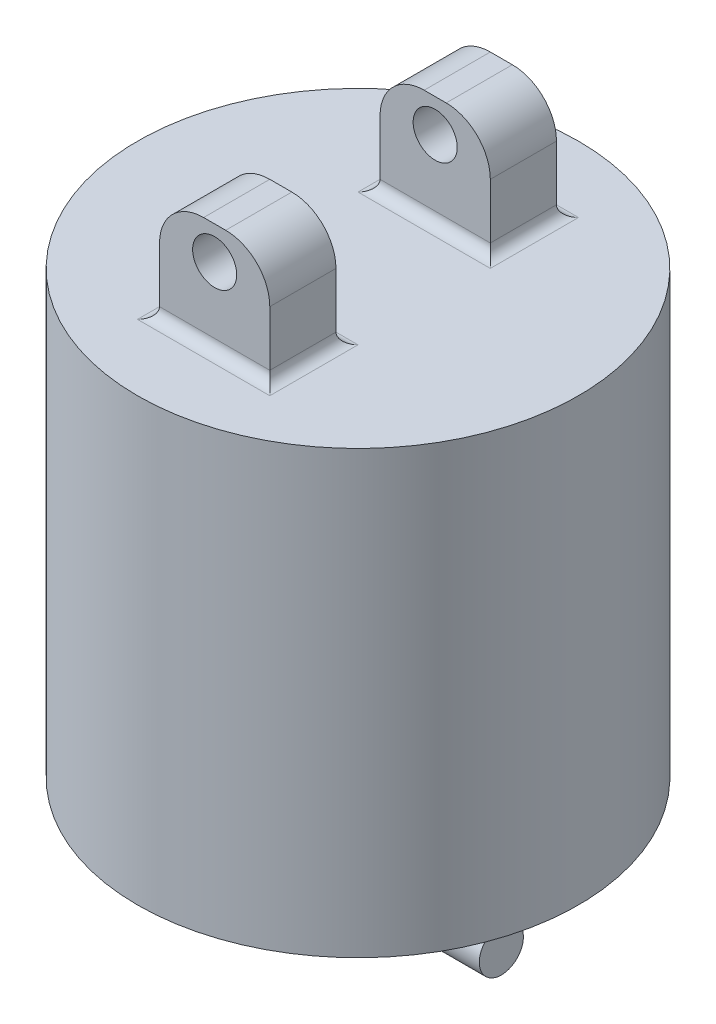
SolidWorks part; units mm, degrees
ref_plane "Front Plane" through (0, 0, 0) normal (0, 0, 1) x (1, 0, 0)
ref_plane "Top Plane" through (0, 0, 0) normal (0, 1, 0) x (1, 0, 0)
ref_plane "Right Plane" through (0, 0, 0) normal (1, 0, 0) x (0, 0, -1)
sketch "Sketch1" plane through (0, 0, 0) normal (0, 1, 0) x (1, 0, 0)
  circle A0 centre (0, 0) radius 50
  dimension "D1" = 100
extrude "Boss-Extrude1" add sketch "Sketch1" along normal blind 100
sketch "Sketch6" plane through (0, 100, 0) normal (0, 1, 0) x (1, 0, 0)
  line L1 (-12.5, -32.5) -> (12.5, -32.5)
  line L2 (-12.5, -32.5) -> (-12.5, -17.5)
  line L3 (-12.5, -17.5) -> (12.5, -17.5)
  line L4 (12.5, -32.5) -> (12.5, -17.5)
  line L5 (-12.5, -32.5) -> (12.5, -17.5) construction
  line L6 (-12.5, -17.5) -> (12.5, -32.5) construction
  point P0 (0, -25)
  dimension "D1" = 25
  dimension "D2" = 15
  dimension "D3" = 0
  dimension "D4" = 25
extrude "Boss-Extrude3" add sketch "Sketch6" along normal blind 25
fillet "Fillet3" radius 2.5 4 edges at (-12.5, 100, 25) (0, 100, 17.5) (0, 100, 32.5) (12.5, 100, 25)
fillet "Fillet4" radius 10 2 edges at (-12.5, 125, 25) (12.5, 125, 25)
sketch "Sketch7" plane through (0, 0, 32.5) normal (0, 0, 1) x (1, 0, 0)
  line L0 (12.5, 115) -> (12.5, 102.5) construction
  line L1 (-2.5, 125) -> (2.5, 125) construction
  circle A0 centre (0, 117.5) radius 5
  dimension "D1" = 10
  dimension "D2" = 12.5
  dimension "D3" = 7.5
extrude "Cut-Extrude2" cut sketch "Sketch7" against normal blind 25
pattern_circular "CirPattern1" count 2 every 180 about axis through (0, 0, 0) along (0, 1, 0) of "Cut-Extrude2", "Boss-Extrude3", "Fillet3", "Fillet4"
sketch "Sketch9" plane through (0, 0, 0) normal (1, 0, 0) x (0, 0, -1)
  line L0 (-50, 0) -> (50, 0) construction
  line L1 (12.5, -25) -> (-12.5, -25)
  line L2 (12.5, -25) -> (12.5, 0)
  line L3 (12.5, 0) -> (-12.5, 0)
  line L4 (-12.5, -25) -> (-12.5, 0)
  line L5 (12.5, -25) -> (-12.5, 0) construction
  line L6 (12.5, 0) -> (-12.5, -25) construction
  line L7 (50, 0) -> (50, 100) construction
  point P0 (0, -12.5)
  dimension "D1" = 0
  dimension "D2" = 25
  dimension "D3" = 25
  dimension "D4" = 50
extrude "Boss-Extrude4" add sketch "Sketch9" along normal blind 15 and the other way blind 15
fillet "Fillet5" radius 2.5 4 edges at (0, 0, 12.5) (-15, 0, 0) (0, 0, -12.5) (15, 0, 0)
fillet "Fillet6" radius 10 2 edges at (0, -25, 12.5) (0, -25, -12.5)
sketch "Sketch10" plane through (0, 0, 0) normal (1, 0, 0) x (0, 0, -1)
  line L0 (-12.5, -2.5) -> (-12.5, -15) construction
  line L1 (-2.5, -25) -> (2.5, -25) construction
  circle A0 centre (0, -17.5) radius 5
  point P6 (0, -25)
  dimension "D1" = 10
  dimension "D2" = 12.5
  dimension "D3" = 7.5
extrude "Boss-Extrude5" add sketch "Sketch10" along normal blind 32.5 and the other way blind 32.5
